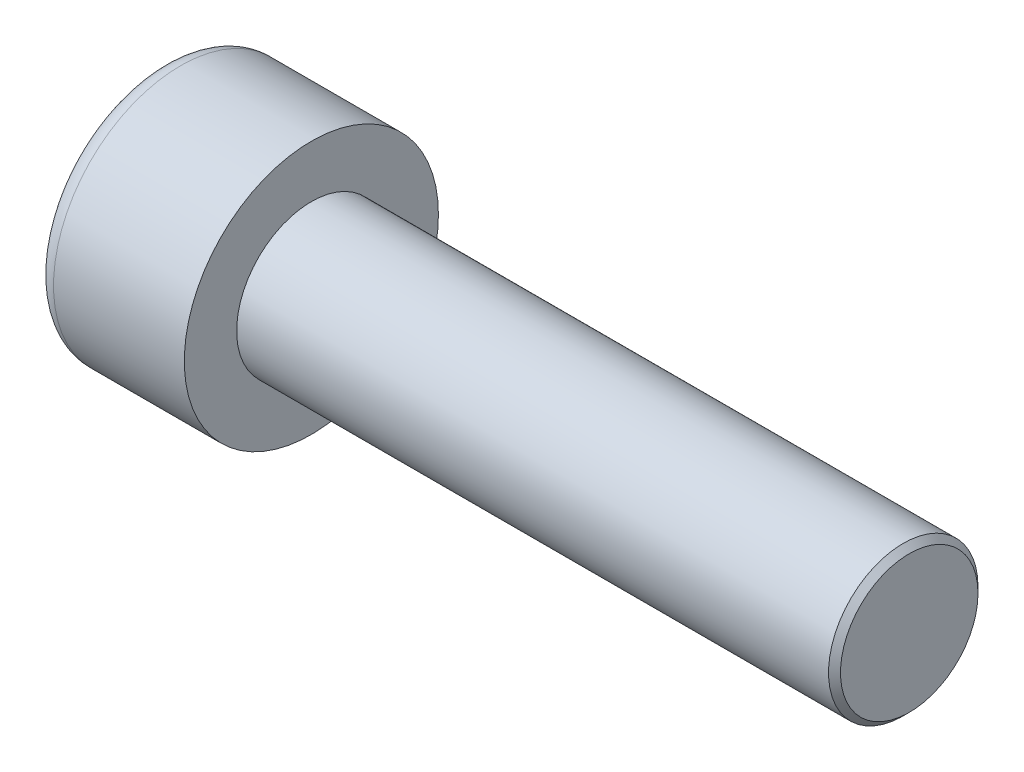
SolidWorks part; units mm, degrees
ref_plane "Front" through (0, 0, 0) normal (0, 0, 1) x (1, 0, 0)
ref_plane "Top" through (0, 0, 0) normal (0, 1, 0) x (1, 0, 0)
ref_plane "Right" through (0, 0, 0) normal (1, 0, 0) x (0, 0, -1)
sketch "Sketch1" plane through (0, 0, 0) normal (1, 0, 0) x (0, 0, -1)
  circle A0 centre (0, 0) radius 4.25
  dimension "dk" = 8.5
extrude "BaseHead" add sketch "Sketch1" along normal blind 5
sketch "Sketch2" plane through (5, 0, 0) normal (1, 0, 0) x (0, 0, -1)
  circle A0 centre (0, 0) radius 2.5
  dimension "d" = 5
extrude "BaseBody" add sketch "Sketch2" along normal blind 20
cosmetic thread "ThreadCosmetic1" parameters "b"=22, "D2"=4.134
sketch "Sketch3" plane through (0, 0, 0) normal (1, 0, 0) x (0, 0, -1)
  line L1 (2.3094, 0) -> (1.1547, 2)
  line L2 (1.1547, 2) -> (-1.1547, 2)
  line L3 (-1.1547, 2) -> (-2.3094, 0)
  line L4 (-2.3094, 0) -> (-1.1547, -2)
  line L5 (-1.1547, -2) -> (1.1547, -2)
  line L6 (1.1547, -2) -> (2.3094, 0)
  circle A0 centre (0, 0) radius 2 construction
  dimension "s" = 4
  dimension "e" = 4.6188
extrude "HexagonSocket" cut sketch "Sketch3" along normal blind 2.5
sketch "Sketch4" plane through (-4.1961, 0.75, 0) normal (0, 0, 1) x (-1, 0, 0)
  line L0 (-6.6961, 2.75) -> (-7.8508, 0.75)
  line L2 (-7.8508, 0.75) -> (-6.6961, 0.75)
  line L3 (-6.6961, 0.75) -> (-6.6961, 2.75)
  line L4 (-5.0351, 0.75) -> (0.839, 0.75) construction
  line L5 (-29.1961, 0.75) -> (-9.1961, 0.75) construction
  line L6 (-9.1961, 0.75) -> (-4.1961, 0.75) construction
  dimension "m" = 60
revolve "Cut-Revolve1" cut sketch "Sketch4" angle 360 about L4
fillet "HeadFillet" [suppressed] radius 0.2
fillet "TopFillet" radius 0.625 1 edges at (0, 0, -4.25)
chamfer "Chamfer1" distance 0.2 angle 45 1 edges at (25, 0, -2.5)
sketch "Sketch5" plane through (0, 0, 0) normal (0, 0, 1) x (1, 0, 0)
  line L0 (24.8, 2.125) -> (25.0165, 2.5)
  line L1 (25.0165, 2.5) -> (25.0165, 2.933)
  line L2 (25.0165, 2.933) -> (24.5835, 2.933)
  line L3 (24.5835, 2.933) -> (24.5835, 2.5)
  line L4 (24.5835, 2.5) -> (24.8, 2.125)
  line L5 (0, 0) -> (7.8886, 0) construction
  line L6 (24.8, -2.5) -> (24.8, 2.5) construction
  dimension "D1" = 5
  dimension "D2" = 0.433
revolve "Cut-Revolve10" [suppressed] cut sketch "Sketch5" angle 360 about L5
pattern_linear "LPattern10" [suppressed] count 42 spacing 0.5196 along (1, 0, 0)
equation "\"r1@TopFillet\" = \"d@Sketch2\" / 8"
equation "\"D1@Chamfer1\" = \"r@HeadFillet\""
equation "\"D1@Sketch5\" = \"d@Sketch2\""
equation "\"D2@Sketch5\" =  ( \"d@Sketch2\" - \"D2@ThreadCosmetic1\" )  / 2"
equation "\"D3@LPattern10\" = \"D2@Sketch5\" * 1.2"
equation "\"D1@LPattern10\" = \"b@ThreadCosmetic1\" / \"D3@LPattern10\""
